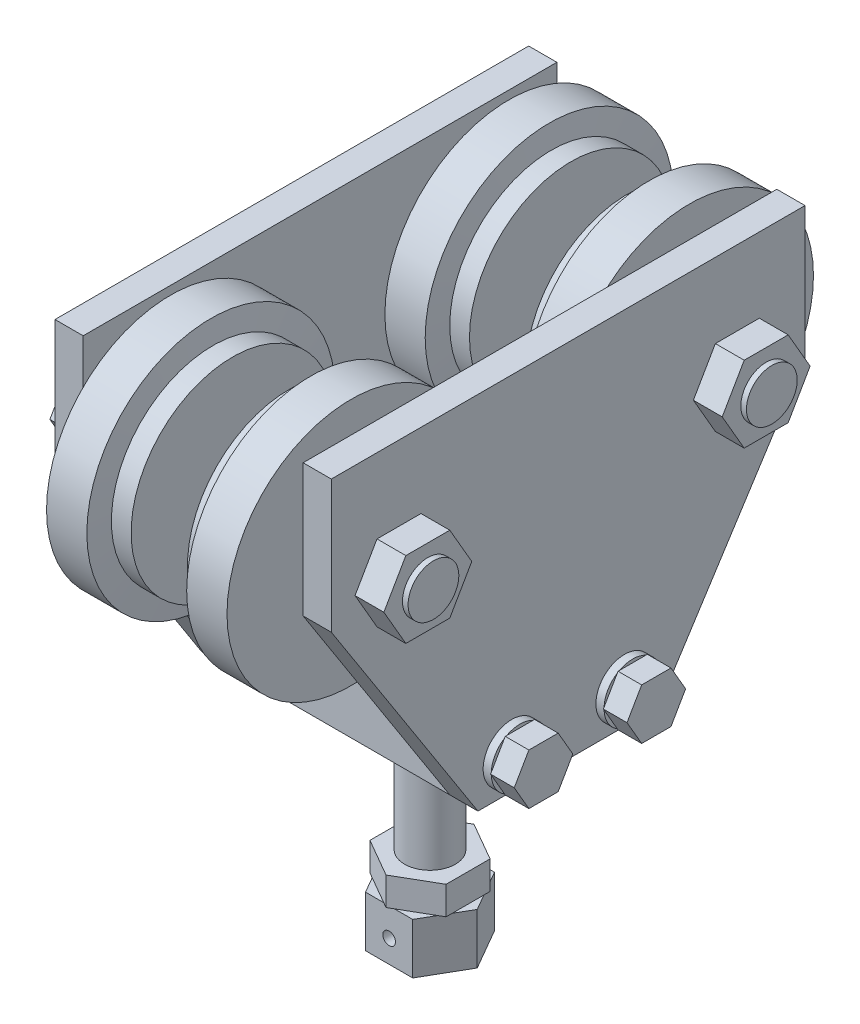
SolidWorks part; units mm, degrees
ref_plane "Front" through (0, 0, 0) normal (0, 0, 1) x (1, 0, 0)
ref_plane "Top" through (0, 0, 0) normal (0, 1, 0) x (1, 0, 0)
ref_plane "Right" through (0, 0, 0) normal (1, 0, 0) x (0, 0, -1)
ref_plane "Z PLANE" through (0, 0, 0) normal (0, 0, 1) x (1, 0, 0)
ref_plane "YOKE BOTTOM" through (0, 0, 0) normal (0, 1, 0) x (-1, 0, 0)
ref_plane "X PLANE" through (0, 0, 0) normal (1, 0, 0) x (0, 0, -1)
sketch "YOKE CROSS SECTION" plane through (0, 0, 0) normal (1, 0, 0) x (0, 0, -1)
  line L0 (0, 0) -> (0, 57.0916) construction
  line L1 (0, 84.8167) -> (0, -84.8167) construction
  line L2 (-50.8, 0) -> (50.8, 0)
  line L3 (69.1602, 0) -> (-69.1602, 0) construction
  line L4 (50.8, 0) -> (50.8, 38.1)
  line L5 (-50.8, 0) -> (-50.8, 38.1)
  line L6 (50.8, 38.1) -> (-50.8, 38.1)
  point P12 (0, 38.1)
  dimension "D1" = 38.1
  dimension "D2" = 101.6
ref_plane "1/2 YOKE LENGTH (A)" through (61.9125, 0, 0) normal (1, 0, 0) x (0, 0, -1)
ref_plane "WHEEL LOCATION" through (0, 0, 95.25) normal (0, 0, 1) x (1, 0, 0)
extrude "YOKE" add sketch "YOKE CROSS SECTION" along normal up to surface (61.9125 mm away) up to plane "1/2 YOKE LENGTH (A)"
sketch "SIDEPLATE PROFILE" plane through (61.9125, 0, 0) normal (1, 0, 0) x (0, 0, -1)
  line L0 (0, 0) -> (50.8, 0)
  line L1 (50.8, 0) -> (133.35, 128.5178)
  line L2 (133.35, 128.5178) -> (133.35, 203.2)
  line L3 (-133.35, 203.2) -> (133.35, 203.2)
  line L4 (-133.35, 128.5178) -> (-133.35, 203.2)
  line L5 (-50.8, 0) -> (-133.35, 128.5178)
  line L6 (0, 0) -> (-50.8, 0)
  line L7 (0, 84.8167) -> (0, -84.8167) construction
  line L8 (69.1602, 0) -> (-69.1602, 0) construction
  dimension "D1" = 50.8
  dimension "D2" = 50.8
  dimension "D3" = 82.55
  dimension "D4" = 82.55
  dimension "D5" = 128.5178
  dimension "D6" = 128.5178
  dimension "D7" = 74.6822
  dimension "D8" = 74.6822
  dimension "D9" = 266.7
ref_plane "WHEEL HEIGHT" through (0, 139.7, 0) normal (0, 1, 0) x (-1, 0, 0)
ref_plane "YOKE SCREW LOCATION Z" through (0, 0, 31.75) normal (0, 0, 1) x (1, 0, 0)
ref_plane "YOKE SCREW LOCATION Y" through (0, 19.05, 0) normal (0, 1, 0) x (-1, 0, 0)
extrude "SIDEPLATE" add sketch "SIDEPLATE PROFILE" along normal blind 15.875
sketch "WHEEL PIN NUT PROFILE" plane through (77.7875, 0, 0) normal (1, 0, 0) x (0, 0, -1)
  line L0 (-95.25, 92.5951) -> (-95.25, -92.5951) construction
  line L1 (-70.5033, 139.7) -> (-82.8767, 161.1312)
  line L2 (-82.8767, 161.1312) -> (-107.6233, 161.1312)
  line L3 (-107.6233, 161.1312) -> (-119.9967, 139.7)
  line L4 (-119.9967, 139.7) -> (-107.6233, 118.2688)
  line L5 (-107.6233, 118.2688) -> (-82.8767, 118.2688)
  line L6 (-82.8767, 118.2688) -> (-70.5033, 139.7)
  line L7 (113.7467, 139.7) -> (-113.7467, 139.7) construction
  circle A0 centre (-95.25, 139.7) radius 13.4938 construction
  dimension "D1" = 42.8625
extrude "WHEEL PIN NUT" add sketch "WHEEL PIN NUT PROFILE" along normal blind 16.2306
sketch "WHEEL PIN PROJECTION PROFILE" plane through (94.0181, 0, 0) normal (1, 0, 0) x (0, 0, -1)
  line L0 (-95.25, 92.5951) -> (-95.25, -92.5951) construction
  line L3 (113.7467, 139.7) -> (-113.7467, 139.7) construction
  circle A0 centre (-95.25, 139.7) radius 14.2875
  dimension "D1" = 28.575
extrude "WHEEL PIN PROJECTION" add sketch "WHEEL PIN PROJECTION PROFILE" along normal blind 3.175
sketch "LOCKNUTS PROFILE" plane through (77.7875, 0, 0) normal (1, 0, 0) x (0, 0, -1)
  line L0 (-31.75, 84.8167) -> (-31.75, -84.8167) construction
  line L1 (50, 19.05) -> (-50, 19.05) construction
  circle A0 centre (-31.75, 19.05) radius 16.129
  dimension "D1" = 32.258
extrude "LOCKNUTS" add sketch "LOCKNUTS PROFILE" along normal blind 4.572
sketch "SCREWS PROFILE" plane through (82.3595, 0, 0) normal (1, 0, 0) x (0, 0, -1)
  line L0 (50, 19.05) -> (-50, 19.05) construction
  line L1 (-15.2522, 19.05) -> (-23.5011, 33.3375)
  line L2 (-23.5011, 33.3375) -> (-39.9989, 33.3375)
  line L3 (-39.9989, 33.3375) -> (-48.2478, 19.05)
  line L4 (-48.2478, 19.05) -> (-39.9989, 4.7625)
  line L5 (-39.9989, 4.7625) -> (-23.5011, 4.7625)
  line L6 (-23.5011, 4.7625) -> (-15.2522, 19.05)
  line L7 (-31.75, 84.8167) -> (-31.75, -84.8167) construction
  circle A0 centre (-31.75, 19.05) radius 14.2875 construction
  dimension "D1" = 28.575
extrude "SCREWS" add sketch "SCREWS PROFILE" along normal blind 13.3096
sketch "PROFILE" plane through (0, 38.1, 0) normal (0, 1, 0) x (-1, 0, 0)
  line L0 (84.8167, 0) -> (-84.8167, 0) construction
  line L1 (0, 83.2389) -> (0, -83.2389) construction
  circle A0 centre (0, 0) radius 22.225
  dimension "D1" = 44.45
extrude "KING BOLT HEAD" add sketch "PROFILE" along normal blind 25.4
mirror "Mirror1" about plane through (0, 0, 0) normal (0, 0, 1) of "WHEEL PIN PROJECTION", "WHEEL PIN NUT"
mirror "Mirror YOKE SCREWS" about plane through (0, 0, 0) normal (0, 0, 1) of "SCREWS", "LOCKNUTS"
mirror "Mirror SIDE 1" about plane through (0, 0, 0) normal (1, 0, 0) of bodies 112
ref_plane "TOP OF NUT" through (0, -83.0521, 0) normal (0, 1, 0) x (-1, 0, 0)
sketch "DIA." plane through (0, 0, 0) normal (0, -1, 0) x (1, 0, 0)
  line L0 (84.8167, 0) -> (-84.8167, 0) construction
  line L1 (0, -83.2389) -> (0, 83.2389) construction
  circle A0 centre (0, 0) radius 14.2875
  dimension "D1" = 28.575
extrude "KING BOLT" add sketch "DIA." along normal up to surface (83.0521 mm away) up to plane "TOP OF NUT"
sketch "KING BOLT JAN NUT PROFILE" plane through (0, -83.0521, 0) normal (0, -1, 0) x (1, 0, 0)
  line L0 (84.8167, 0) -> (-84.8167, 0) construction
  line L1 (0, -24.754) -> (21.4376, -12.377)
  line L2 (21.4376, -12.377) -> (21.4376, 12.377)
  line L3 (21.4376, 12.377) -> (0, 24.754)
  line L4 (0, 24.754) -> (-21.4376, 12.377)
  line L5 (-21.4376, 12.377) -> (-21.4376, -12.377)
  line L6 (-21.4376, -12.377) -> (0, -24.754)
  line L7 (0, -83.2389) -> (0, 83.2389) construction
  circle A0 centre (0, 0) radius 21.4376 construction
  dimension "D1" = 42.8752
extrude "KING BOLT JAM NUT" add sketch "KING BOLT JAN NUT PROFILE" along normal blind 15.875
sketch "KING BOLT NUT PROFILE" plane through (0, -98.9271, 0) normal (0, -1, 0) x (1, 0, 0)
  line L1 (26.5798, 0) -> (13.2899, 23.0188)
  line L2 (13.2899, 23.0188) -> (-13.2899, 23.0188)
  line L3 (-13.2899, 23.0188) -> (-26.5798, 0)
  line L4 (-26.5798, 0) -> (-13.2899, -23.0187)
  line L5 (-13.2899, -23.0187) -> (13.2899, -23.0187)
  line L6 (13.2899, -23.0187) -> (26.5798, 0)
  line L10 (0, -83.2389) -> (0, 83.2389) construction
  line L11 (84.8167, 0) -> (-84.8167, 0) construction
  circle A0 centre (0, 0) radius 23.0188 construction
  dimension "D1" = 46.0375
extrude "KING BOLT NUT" add sketch "KING BOLT NUT PROFILE" along normal blind 28.575
sketch "Sketch5" plane through (0, -127.5021, 0) normal (0, -1, 0) x (1, 0, 0)
  circle A0 centre (0, 0) radius 14.2875 construction
  circle A1 centre (0, 0) radius 14.2875
extrude "EXTENDED KING BOLT" add sketch "Sketch5" along normal blind 6.35
chamfer "Chamfer1" distance 2.3812 angle 45 1 edges at (0, -133.8521, -14.2875)
ref_plane "MOUNTING REF PLANE" through (0, -34.925, 0) normal (0, 1, 0) x (-1, 0, 0)
sketch "Sketch6" plane through (0, 0, 95.25) normal (0, 0, 1) x (1, 0, 0)
  line L0 (15.875, 139.7) -> (61.9125, 139.7)
  line L1 (50.8, 158.75) -> (61.9125, 158.75)
  line L2 (15.875, 139.7) -> (15.875, 196.85)
  line L3 (50.8, 158.75) -> (50.8, 209.55)
  line L4 (26.9875, 196.85) -> (28.1051, 209.55)
  line L5 (26.9875, 196.85) -> (15.875, 196.85)
  line L6 (50.8, 209.55) -> (28.1051, 209.55)
  line L7 (61.9125, 139.7) -> (61.9125, 158.75)
  line L8 (113.7467, 139.7) -> (-113.7467, 139.7) construction
  line L9 (61.9125, -75.0522) -> (61.9125, 75.0522) construction
  dimension "D11" = 46.0375
  dimension "D10" = 34.925
  dimension "D1" = 57.15
  dimension "D2" = 57.15
  dimension "D3" = 69.85
  dimension "D4" = 69.85
  dimension "D5" = 19.05
  dimension "D6" = 19.05
  dimension "D7" = 11.1125
  dimension "D8" = 11.1125
  dimension "D9" = 33.8074
  dimension "D12" = 46.0375
revolve "WHEEL" add sketch "Sketch6" angle 360 about axis through (97.1931, 139.7, 95.25) along (-1, 0, 0)
mirror "Mirror2" about plane through (0, 0, 0) normal (0, 0, 1) of "WHEEL"
mirror "Mirror3" about plane through (0, 0, 0) normal (1, 0, 0) of "Mirror2", "WHEEL"
sketch "Sketch7" plane through (0, 0, 23.0188) normal (0, 0, 1) x (1, 0, 0)
  line L0 (0, -83.2389) -> (0, 83.2389) construction
  line L1 (-13.2899, -127.5021) -> (-26.5798, -127.5021) construction
  circle A0 centre (0, -114.8021) radius 3.5719
  dimension "D2" = 7.1437
  dimension "D1" = 12.7
extrude "COTTER PIN HOLE" cut sketch "Sketch7" against normal up to next
sketch "Sketch8" plane through (0, 0, 0) normal (0, -1, 0) x (1, 0, 0)
  circle A0 centre (0, 0) radius 25.4
  circle A1 centre (0, 0) radius 30.1625
  dimension "D1" = 50.8
  dimension "D2" = 60.325
extrude "SPACER" [suppressed] add sketch "Sketch8" along normal blind 12.7
ref_plane "TREAD OF TRACK" through (0, 82.55, 0) normal (0, 1, 0) x (-1, 0, 0)
